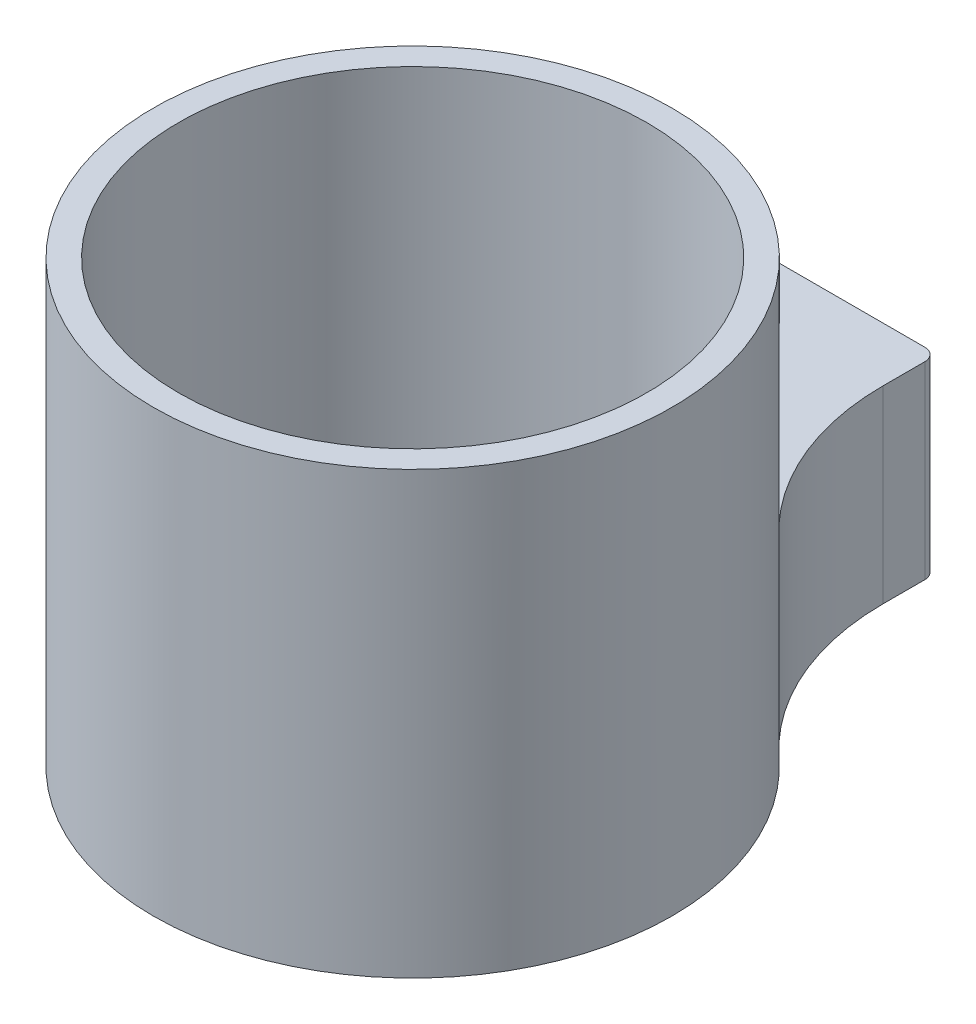
SolidWorks part; units mm, degrees
ref_plane "Plan de face" through (0, 0, 0) normal (0, 0, 1) x (1, 0, 0)
ref_plane "Plan de dessus" through (0, 0, 0) normal (0, 1, 0) x (1, 0, 0)
ref_plane "Plan de droite" through (0, 0, 0) normal (1, 0, 0) x (0, 0, -1)
sketch "Esquisse1" plane through (0, 0, 0) normal (0, 0, 1) x (1, 0, 0)
  line L1 (-7.5, -7.5) -> (7.5, -7.5)
  line L2 (-7.5, -7.5) -> (-7.5, 7.5)
  line L3 (-7.5, 7.5) -> (7.5, 7.5)
  line L4 (7.5, -7.5) -> (7.5, 7.5)
  line L5 (-7.5, -7.5) -> (7.5, 7.5) construction
  line L6 (-7.5, 7.5) -> (7.5, -7.5) construction
  point P0 (0, 0)
  dimension "D1" = 15
  dimension "D2" = 15
extrude "Boss.-Extru.1" add sketch "Esquisse1" along normal blind 15
hole_wizard "Trous de centrage Ø5.0mm1" positions "Esquisse2" profile "Esquisse3" hole size "Ø5.0" standard "AS"
sketch "Esquisse2" plane through (0, 0, 0) normal (0, 0, -1) x (-1, 0, 0)
  line L0 (0, 19.25) -> (0, -19.25) construction
  line L1 (22.55, 0) -> (-22.55, 0) construction
  point P0 (0, 0)
sketch "Esquisse3" plane through (0, 0, 0) normal (1, 0, 0) x (0, 1, 0)
  line L0 (0, 0) -> (0, 11.9228)
  line L1 (0, 11.9228) -> (3.2, 10)
  line L2 (3.2, 10) -> (3.2, 0)
  line L5 (3.2, 0) -> (0, 0)
  line L10 (0, 11.9228) -> (-3.2, 10) construction
  line L11 (0, -6.35) -> (0, 107.95) construction
  dimension "Diamètre du perçage" = 6.4
  dimension "Profondeur du perçage" = 10
  dimension "Angle de pointe" = 118
sketch "Esquisse4" plane through (0, 7.5, 0) normal (0, 1, 0) x (1, 0, 0)
  circle A0 centre (0, -34.1862) radius 20.6
  circle A1 centre (0, -34.1862) radius 18.6
  dimension "D1" = 37.2
  dimension "D2" = 2
extrude "Boss.-Extru.2" add sketch "Esquisse4" along normal blind 20 and the other way blind 10
sketch "Esquisse5" plane through (0, -2.5, 0) normal (0, -1, 0) x (1, 0, 0)
  line L1 (-7.5, 15) -> (7.5, 15)
  line L2 (-7.5, 15) -> (7.5, 15)
  circle A0 centre (0, 34.1862) radius 16
  arc A1 (7.5, 15) -> (-7.5, 15) centre (0, 34.1862) ccw
  arc A2 (7.5, 15) -> (-7.5, 15) centre (0, 34.1862) ccw
  dimension "D2" = 32
  dimension "D1" = 0
extrude "Boss.-Extru.3" add sketch "Esquisse5" along normal up to surface (5 mm away) up to face at (0, -7.5, 7.5)
fillet "Congé1" radius 20 2 edges at (-7.5, 0, 15) (7.5, 0, 15)
fillet "Congé2" radius 1 2 edges at (-7.5, 0, 0) (7.5, 0, 0)
hole_wizard "Trous de centrage Ø1.0mm1" positions "Esquisse6" profile "Esquisse7" hole size "Ø1.0" standard "ISO" end condition through all
sketch "Esquisse6" plane through (0, 7.5, 0) normal (0, 1, 0) x (1, 0, 0)
  arc A4 (13.9532, -19.0314) -> (-13.9532, -19.0314) centre (0, -34.1862) ccw construction
  point P0 (6, -13.5404)
  point P19 (6, -12.599)
  dimension "D1" = 21.5
  dimension "D2" = 6
sketch "Esquisse7" plane through (6, 7.5, 13.5404) normal (1, 0, 0) x (0, 0, 1)
  line L0 (0, 0) -> (0, 15)
  line L1 (0, 15) -> (0.5, 15)
  line L2 (0.5, 15) -> (0.5, 0)
  line L5 (0.5, 0) -> (0, 0)
  line L11 (0, -6.35) -> (0, 107.95) construction
  dimension "Diamètre du perçage jusqu'au prochain" = 1
  dimension "Profondeur du perçage jusqu'au prochain" = 15
